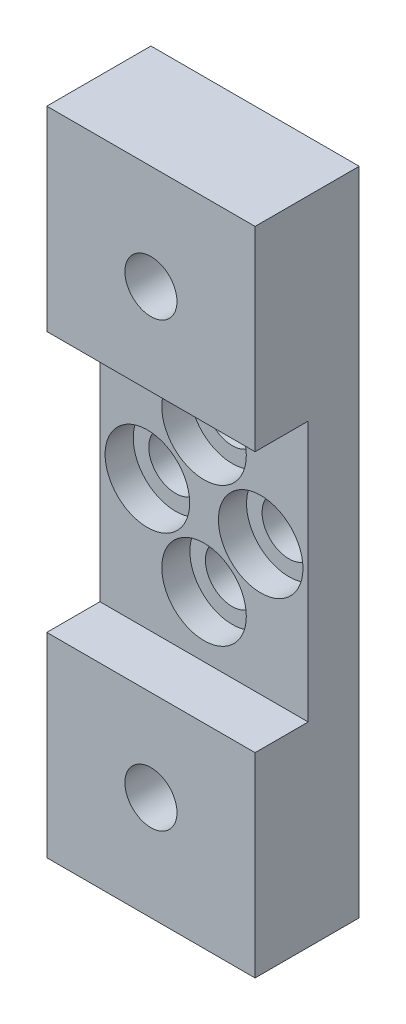
SolidWorks part; units mm, degrees
material "6061 Alloy"
ref_plane "Front Plane" through (0, 0, 0) normal (0, 0, 1) x (1, 0, 0)
ref_plane "Top Plane" through (0, 0, 0) normal (0, 1, 0) x (1, 0, 0)
ref_plane "Right Plane" through (0, 0, 0) normal (1, 0, 0) x (0, 0, -1)
sketch "Sketch1" plane through (0, 0, 0) normal (0, 0, 1) x (1, 0, 0)
  line L1 (-29.7745, 41.7474) -> (-4.3745, 41.7474)
  line L2 (-29.7745, 41.7474) -> (-29.7745, -37.6276)
  line L3 (-29.7745, -37.6276) -> (-4.3745, -37.6276)
  line L4 (-4.3745, 41.7474) -> (-4.3745, -37.6276)
  dimension "D1" = 25.4
  dimension "D2" = 79.375
extrude "Extrude1" add sketch "Sketch1" along normal blind 12.7
sketch "Sketch2" plane through (0, 0, 12.7) normal (0, 0, 1) x (1, 0, 0)
  line L2 (-29.7745, -13.8278) -> (-4.3745, -13.8278)
  line L3 (-29.7745, -13.8278) -> (-4.3745, -13.8278)
  line L4 (-4.3745, 17.9476) -> (-4.3745, -13.8278)
  line L5 (-29.7745, 17.9476) -> (-4.3745, 17.9476)
  line L6 (-29.7745, 17.9476) -> (-4.3745, 17.9476)
  line L7 (-29.7745, 17.9476) -> (-29.7745, -13.8278)
  line L8 (-29.7745, -13.8278) -> (-29.8783, -13.6291)
  line M3 (-29.7745, 41.7474) -> (-29.7745, -37.6276)
  line M5 (-4.3745, -37.6276) -> (-4.3745, 41.7474)
  dimension "D1" = 23.7998
  dimension "D2" = 55.5752
extrude "Cut-Extrude1" cut sketch "Sketch2" against normal blind 6.477 contours L6 L3 M5 M3
sketch "Sketch3" plane through (0, 0, 12.7) normal (0, 0, 1) x (1, 0, 0)
  line L2 (-29.7745, 2.0599) -> (-4.3745, 2.0599)
  line L3 (-29.7745, -13.8278) -> (-29.7745, 17.9476) construction
  line L4 (-4.3745, 17.9476) -> (-4.3745, -13.8278) construction
  line L6 (-29.7745, -6.4364) -> (-4.3745, -6.4364)
  line L7 (-23.9833, -13.8278) -> (-23.9833, 17.9476)
  line L8 (-23.9833, -13.8278) -> (-23.9833, 17.9476)
  line L10 (-10.1657, 17.9476) -> (-10.1657, -13.8278)
  line L11 (-10.1657, 17.9476) -> (-10.1657, -13.8278)
  line L12 (-29.7745, -6.4364) -> (-4.3745, -6.4364)
  line L14 (-29.7745, 10.5562) -> (-4.3745, 10.5562)
  line L15 (-29.7745, 10.5562) -> (-4.3745, 10.5562)
  circle A0 centre (-17.0745, -24.9276) radius 3.175
  circle A1 centre (-17.0745, 29.0474) radius 3.175
  circle A2 centre (-10.1657, 2.0599) radius 3.2639
  circle A3 centre (-23.9833, 2.0599) radius 3.2639
  circle A4 centre (-17.0745, -6.4364) radius 3.2639
  circle A5 centre (-17.0745, 10.5562) radius 3.2639
  dimension "D3" = 31.1912
  dimension "D1" = 5.7912
  dimension "D2" = 5.7912
  dimension "D4" = 48.1838
extrude "Cut-Extrude2" cut sketch "Sketch3" against normal through all contours L15 A5 | L15 A5 | L2 A3 L8 | L8 A3 L2 | L2 A3 L8 | L8 A3 L2 | L11 A2 L2 | L2 A2 L11 | L11 A2 L2 | L2 A2 L11 | L12 A4 | L12 A4 | A0 | A1
sketch "Sketch4" plane through (0, 0, 6.223) normal (0, 0, 1) x (1, 0, 0)
  circle A0 centre (-17.0745, 10.5562) radius 5.1562
  circle A1 centre (-10.1657, 2.0599) radius 5.1562
  circle A2 centre (-17.0745, -6.4364) radius 5.1562
  circle A3 centre (-23.9833, 2.0599) radius 5.1562
extrude "Cut-Extrude3" cut sketch "Sketch4" against normal blind 3.429
